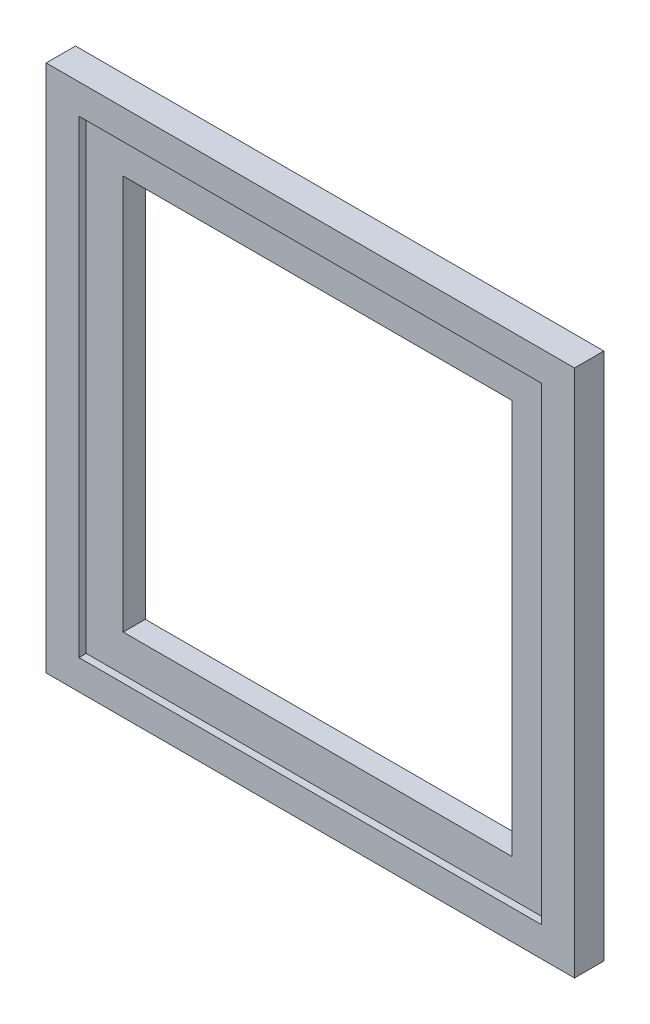
SolidWorks part; units mm, degrees
ref_plane "Front Plane" through (0, 0, 0) normal (0, 0, 1) x (1, 0, 0)
ref_plane "Top Plane" through (0, 0, 0) normal (0, 1, 0) x (1, 0, 0)
ref_plane "Right Plane" through (0, 0, 0) normal (1, 0, 0) x (0, 0, -1)
sketch "Sketch1" plane through (0, 0, 0) normal (0, 0, 1) x (1, 0, 0)
  line L1 (-11.0682, 64.919) -> (103.2318, 64.919)
  line L2 (-11.0682, 64.919) -> (-11.0682, -49.381)
  line L3 (-11.0682, -49.381) -> (103.2318, -49.381)
  line L4 (103.2318, 64.919) -> (103.2318, -49.381)
  dimension "D1" = 114.3
  dimension "D2" = 114.3
extrude "Boss-Extrude1" add sketch "Sketch1" along normal blind 6.35
sketch "Sketch2" plane through (0, 0, 6.35) normal (0, 0, 1) x (1, 0, 0)
  line L0 (103.2318, 37.9951) -> (96.1418, 37.9951) construction
  line L1 (-3.9782, 58.494) -> (96.1418, 58.494)
  line L2 (-3.9782, 58.494) -> (-3.9782, -42.956)
  line L3 (-3.9782, -42.956) -> (96.1418, -42.956)
  line L4 (96.1418, 58.494) -> (96.1418, -42.956)
  line L6 (103.2318, -49.381) -> (103.2318, 64.919) construction
  line L8 (75.1731, 64.919) -> (75.1731, 58.494) construction
  line L9 (103.2318, 64.919) -> (-11.0682, 64.919) construction
  dimension "D1" = 101.45
  dimension "D2" = 100.12
  dimension "D3" = 7.09
  dimension "D4" = 6.425
extrude "Cut-Extrude1" cut sketch "Sketch2" against normal blind 1.5748
sketch "Sketch3" plane through (0, 0, 4.7752) normal (0, 0, 1) x (1, 0, 0)
  line L1 (-3.9782, 58.494) -> (96.1418, 58.494) construction
  line L2 (-3.9782, 58.494) -> (-3.9782, -42.956) construction
  line L3 (-3.9782, -42.956) -> (96.1418, -42.956) construction
  line L4 (96.1418, 58.494) -> (96.1418, -42.956) construction
sketch "Sketch4" plane through (0, 0, 4.7752) normal (0, 0, 1) x (1, 0, 0)
  line L0 (4.0218, 50.494) -> (4.0218, -34.956)
  line L1 (-3.9782, 58.494) -> (96.1418, 58.494) construction
  line L2 (-3.9782, 58.494) -> (-3.9782, -42.956) construction
  line L3 (-3.9782, -42.956) -> (96.1418, -42.956) construction
  line L4 (96.1418, 58.494) -> (96.1418, -42.956) construction
  line L5 (4.0218, -34.956) -> (88.1418, -34.956)
  line L6 (88.1418, 50.494) -> (88.1418, -34.956)
  line L7 (4.0218, 50.494) -> (88.1418, 50.494)
  dimension "D1" = 8
extrude "Cut-Extrude3" cut sketch "Sketch4" against normal through all both and the other way through all
